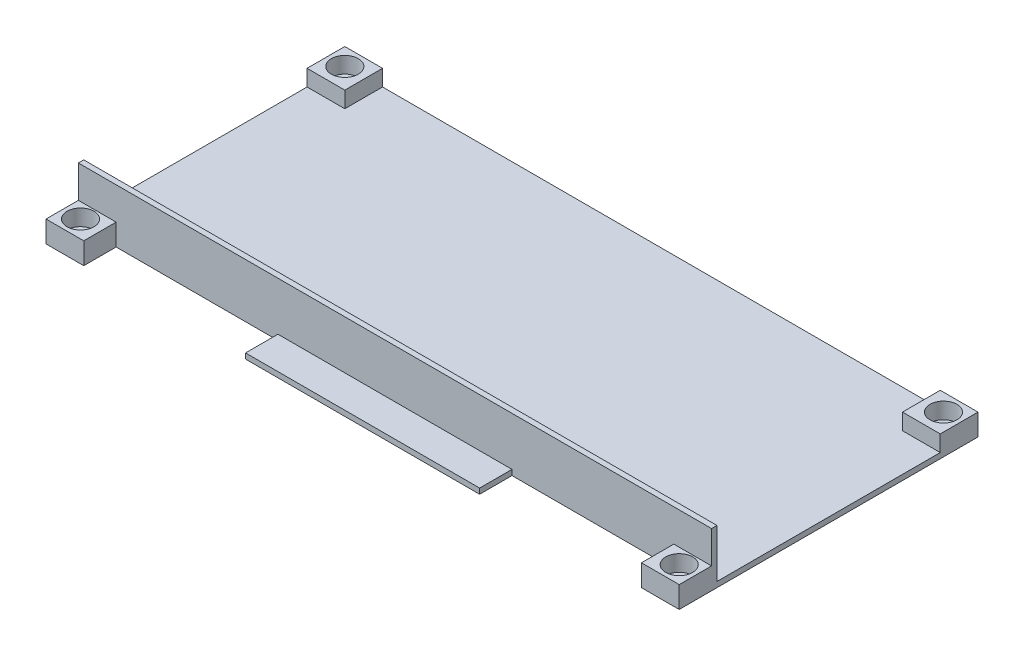
SolidWorks part; units mm, degrees
ref_plane "Front Plane" through (0, 0, 0) normal (0, 0, 1) x (1, 0, 0)
ref_plane "Top Plane" through (0, 0, 0) normal (0, 1, 0) x (1, 0, 0)
ref_plane "Right Plane" through (0, 0, 0) normal (1, 0, 0) x (0, 0, -1)
sketch "Sketch1" plane through (0, 0, 0) normal (0, 1, 0) x (1, 0, 0)
  line L1 (-58.7, -27.7) -> (58.7, -27.7)
  line L2 (-58.7, -27.7) -> (-58.7, 27.7)
  line L3 (-58.7, 27.7) -> (58.7, 27.7)
  line L4 (58.7, -27.7) -> (58.7, 27.7)
  line L5 (-58.7, -27.7) -> (58.7, 27.7) construction
  line L6 (-58.7, 27.7) -> (58.7, -27.7) construction
  point P0 (0, 0)
  dimension "D1" = 55.4
  dimension "D2" = 117.4
extrude "Boss-Extrude1" add sketch "Sketch1" along normal blind 1
sketch "Sketch2" plane through (0, 1, 0) normal (0, 1, 0) x (1, 0, 0)
  line L0 (0, 27.7) -> (0, -27.7) construction
  line L1 (58.7, 27.7) -> (-58.7, 27.7) construction
  line L2 (-58.7, -27.7) -> (58.7, -27.7) construction
  line L3 (-58.7, 0) -> (58.7, 0) construction
  line L4 (-58.7, 27.7) -> (-58.7, -27.7) construction
  line L5 (58.7, -27.7) -> (58.7, 27.7) construction
  line L6 (58.7, 20.7) -> (51.7, 20.7)
  line L7 (-58.7, 27.7) -> (-51.7, 27.7)
  line L8 (-58.7, 27.7) -> (-58.7, 20.7)
  line L9 (-58.7, 20.7) -> (-51.7, 20.7)
  line L10 (-51.7, 27.7) -> (-51.7, 20.7)
  line L11 (51.7, 27.7) -> (51.7, 20.7)
  line L12 (58.7, 27.7) -> (51.7, 27.7)
  line L13 (58.7, 27.7) -> (58.7, 20.7)
  line L14 (58.7, -27.7) -> (58.7, -20.7)
  line L15 (58.7, -27.7) -> (51.7, -27.7)
  line L16 (51.7, -27.7) -> (51.7, -20.7)
  line L17 (58.7, -20.7) -> (51.7, -20.7)
  line L18 (-58.7, -20.7) -> (-51.7, -20.7)
  line L19 (-51.7, -27.7) -> (-51.7, -20.7)
  line L20 (-58.7, -27.7) -> (-51.7, -27.7)
  line L21 (-58.7, -27.7) -> (-58.7, -20.7)
  dimension "D1" = 7
extrude "Boss-Extrude2" add sketch "Sketch2" along normal blind 3
sketch "Sketch3" plane through (0, 4, 0) normal (0, 1, 0) x (1, 0, 0)
  line L1 (-55.5, -24.5) -> (55.5, -24.5) construction
  line L2 (-55.5, -24.5) -> (-55.5, 24.5) construction
  line L3 (-55.5, 24.5) -> (55.5, 24.5) construction
  line L4 (55.5, -24.5) -> (55.5, 24.5) construction
  line L5 (-55.5, -24.5) -> (55.5, 24.5) construction
  line L6 (-55.5, 24.5) -> (55.5, -24.5) construction
  circle A0 centre (-55.5, 24.5) radius 1.35
  circle A1 centre (55.5, 24.5) radius 1.35
  circle A2 centre (55.5, -24.5) radius 1.35
  circle A3 centre (-55.5, -24.5) radius 1.35
  point P0 (0, 0)
  dimension "D3" = 2.7
  dimension "D1" = 49
  dimension "D2" = 111
extrude "Cut-Extrude1" cut sketch "Sketch3" against normal through all
sketch "Sketch7" plane through (0, 0, 0) normal (0, -1, 0) x (1, 0, 0)
  line L0 (0, 0) -> (0, 27.7) construction
  line L1 (51.7, 27.7) -> (21.7, 27.7)
  line L2 (51.7, 27.7) -> (51.7, 21.7)
  line L3 (51.7, 21.7) -> (21.7, 21.7)
  line L4 (21.7, 27.7) -> (21.7, 21.7)
  line L5 (-58.7, 27.7) -> (58.7, 27.7) construction
  line L6 (-21.7, 27.7) -> (-21.7, 21.7)
  line L7 (-51.7, 21.7) -> (-21.7, 21.7)
  line L8 (-51.7, 27.7) -> (-51.7, 21.7)
  line L9 (-51.7, 27.7) -> (-21.7, 27.7)
  point P8 (0, 18.0247)
  dimension "D1" = 30
  dimension "D2" = 6
extrude "Cut-Extrude5" cut sketch "Sketch7" against normal through all
sketch "Sketch9" plane through (0, 4, 0) normal (0, 1, 0) x (1, 0, 0)
  circle A0 centre (-55.5, 24.5) radius 2.5
  circle A1 centre (55.5, 24.5) radius 2.5
  circle A2 centre (55.5, -24.5) radius 2.5
  circle A3 centre (-55.5, -24.5) radius 2.5
  dimension "D1" = 5
extrude "Cut-Extrude6" cut sketch "Sketch9" against normal offset from surface (3 mm away) 1 up to face at (0, 0, 16.4667)
sketch "Sketch10" plane through (0, 1, 0) normal (0, 1, 0) x (1, 0, 0)
  line L0 (58.7, -20.7) -> (58.7, 20.7) construction
  line L1 (58.7, -21.7) -> (-58.7, -21.7)
  line L2 (58.7, -21.7) -> (58.7, -20.7)
  line L3 (58.7, -20.7) -> (-58.7, -20.7)
  line L4 (-58.7, -21.7) -> (-58.7, -20.7)
  line L5 (-58.7, 20.7) -> (-58.7, -20.7) construction
  line L7 (-21.7, -27.7) -> (21.7, -27.7) construction
  dimension "D1" = 1
  dimension "D2" = 6
extrude "Boss-Extrude3" add sketch "Sketch10" along normal blind 9
